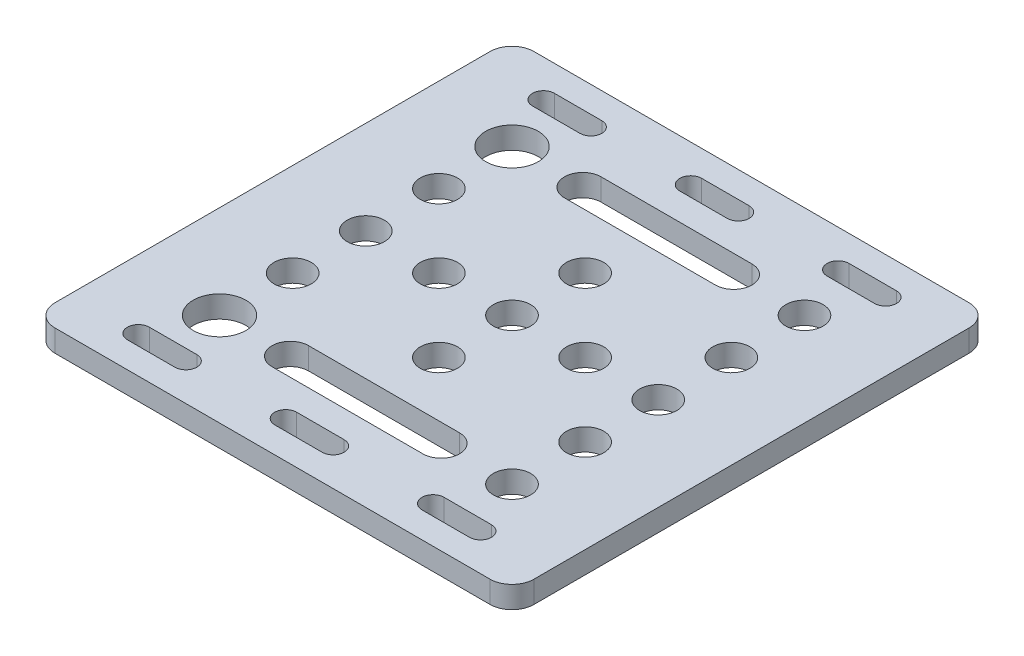
SolidWorks part; units mm, degrees
ref_plane "Front Plane" through (0, 0, 0) normal (0, 0, 1) x (1, 0, 0)
ref_plane "Top Plane" through (0, 0, 0) normal (0, 1, 0) x (1, 0, 0)
ref_plane "Right Plane" through (0, 0, 0) normal (1, 0, 0) x (0, 0, -1)
sketch "Sketch1" plane through (0, 0, 0) normal (0, 1, 0) x (1, 0, 0)
  line L0 (0, -32.75) -> (0, 32.75) construction
  line L1 (32.75, -32.75) -> (-32.75, -32.75)
  line L2 (32.75, -32.75) -> (32.75, 32.75)
  line L3 (32.75, 32.75) -> (-32.75, 32.75)
  line L4 (-32.75, -32.75) -> (-32.75, 32.75)
  line L5 (32.75, -32.75) -> (-32.75, 32.75) construction
  line L6 (32.75, 32.75) -> (-32.75, -32.75) construction
  line L7 (3.25, 29.2) -> (-3.25, 29.2)
  line L8 (3.25, 29.2) -> (3.25, 26.2)
  line L9 (3.25, 26.2) -> (-3.25, 26.2)
  line L10 (-3.25, 29.2) -> (-3.25, 26.2)
  line L11 (3.25, 29.2) -> (-3.25, 26.2) construction
  line L12 (3.25, 26.2) -> (-3.25, 29.2) construction
  line L13 (10.32, 22.5) -> (-10.32, 22.5)
  line L14 (10.32, 22.5) -> (10.32, 17.5)
  line L15 (10.32, 17.5) -> (-10.32, 17.5)
  line L16 (-10.32, 22.5) -> (-10.32, 17.5)
  line L17 (10.32, 22.5) -> (-10.32, 17.5) construction
  line L18 (10.32, 17.5) -> (-10.32, 22.5) construction
  line L19 (32.75, 0) -> (-32.75, 0) construction
  line L20 (10.32, -17.5) -> (-10.32, -17.5)
  line L21 (-10.32, -22.5) -> (-10.32, -17.5)
  line L22 (10.32, -22.5) -> (-10.32, -22.5)
  line L23 (10.32, -22.5) -> (10.32, -17.5)
  line L24 (3.25, -26.2) -> (-3.25, -26.2)
  line L25 (-3.25, -29.2) -> (-3.25, -26.2)
  line L26 (3.25, -29.2) -> (-3.25, -29.2)
  line L27 (3.25, -29.2) -> (3.25, -26.2)
  line L28 (-16.9, 29.2) -> (-16.9, 26.2)
  line L29 (-16.9, 29.2) -> (-23.4, 29.2)
  line L30 (-23.4, 29.2) -> (-23.4, 26.2)
  line L31 (-16.9, 26.2) -> (-23.4, 26.2)
  line L32 (23.4, 29.2) -> (23.4, 26.2)
  line L33 (23.4, 29.2) -> (16.9, 29.2)
  line L34 (16.9, 29.2) -> (16.9, 26.2)
  line L35 (23.4, 26.2) -> (16.9, 26.2)
  line L36 (23.4, -29.2) -> (16.9, -29.2)
  line L37 (16.9, -29.2) -> (16.9, -26.2)
  line L38 (23.4, -26.2) -> (16.9, -26.2)
  line L39 (23.4, -29.2) -> (23.4, -26.2)
  line L40 (-16.9, -29.2) -> (-23.4, -29.2)
  line L41 (-23.4, -29.2) -> (-23.4, -26.2)
  line L42 (-16.9, -26.2) -> (-23.4, -26.2)
  line L43 (-16.9, -29.2) -> (-16.9, -26.2)
  line L44 (20, 32.75) -> (20, 19.4093) construction
  line L45 (20, 20) -> (10.32, 20) construction
  line L46 (-20, 27.7) -> (-20, 20) construction
  line L47 (-20, 20) -> (-12.82, 20) construction
  circle A0 centre (0, 10) radius 2.55
  circle A1 centre (-3.25, 27.7) radius 1.5
  circle A2 centre (3.25, 27.7) radius 1.4915
  circle A3 centre (-10.32, 20) radius 2.5
  circle A4 centre (10.32, 20) radius 2.5
  circle A5 centre (0, -10) radius 2.55
  circle A6 centre (10.32, -20) radius 2.5
  circle A7 centre (-10.32, -20) radius 2.5
  circle A8 centre (3.25, -27.7) radius 1.4915
  circle A9 centre (-3.25, -27.7) radius 1.5
  circle A10 centre (0, 0) radius 2.55
  circle A11 centre (-23.4, 27.7) radius 1.5
  circle A12 centre (-16.9, 27.7) radius 1.4915
  circle A13 centre (16.9, 27.7) radius 1.5
  circle A14 centre (23.4, 27.7) radius 1.4915
  circle A15 centre (23.4, -27.7) radius 1.4915
  circle A16 centre (16.9, -27.7) radius 1.5
  circle A17 centre (-16.9, -27.7) radius 1.4915
  circle A18 centre (-23.4, -27.7) radius 1.5
  circle A19 centre (20, 20) radius 2.55
  circle A20 centre (20, 10) radius 2.55
  circle A21 centre (20, 0) radius 2.55
  circle A22 centre (20, -10) radius 2.55
  circle A23 centre (20, -20) radius 2.55
  circle A24 centre (-20, 20) radius 3.6
  circle A25 centre (-20, 10) radius 2.55
  circle A26 centre (-20, -10) radius 2.55
  circle A27 centre (-20, -20) radius 3.6
  circle A28 centre (-20, 0) radius 2.55
  circle A29 centre (10, 0) radius 2.55
  circle A30 centre (0, 0) radius 2.55
  circle A31 centre (-10, 0) radius 2.55
  point P0 (0, 0)
  point P6 (0, 27.7)
  point P11 (0, 20)
  dimension "D12" = 5.1
  dimension "D13" = 32.75
  dimension "D14" = 3
  dimension "D15" = 2.983
  dimension "D16" = 5
  dimension "D17" = 5
  dimension "D18" = 5.1
  dimension "D20" = 9.35
  dimension "D21" = 2
  dimension "D22" = 9.35
  dimension "D23" = 5.1
  dimension "D25" = 10
  dimension "D26" = 7.2
  dimension "D27" = 4
  dimension "D28" = 10
  dimension "D1" = 65.5
  dimension "D2" = 65.5
  dimension "D3" = 6.5
  dimension "D4" = 3
  dimension "D5" = 3.55
  dimension "D6" = 32.75
  dimension "D7" = 3.7
  dimension "D8" = 20.64
  dimension "D9" = 5
  dimension "D10" = 32.75
  dimension "D11" = 10
  dimension "D19" = 2
  dimension "D24" = 5
extrude "Boss-Extrude1" add sketch "Sketch1" along normal blind 3 contours L4 L1 L2 L3 A27 A26 L40 A18 L42 L43 A17 L36 A16 L38 L39 A15 L26 A9 L24 L27 A8 L22 A7 L20 A6 A5 A4 L15 A3 L13 A2 L8 L9 A1 L7 A0
fillet "Fillet2" radius 3 4 edges at (-32.75, 1.5, 32.75) (32.75, 1.5, 32.75) (-32.75, 1.5, -32.75) (32.75, 1.5, -32.75)
